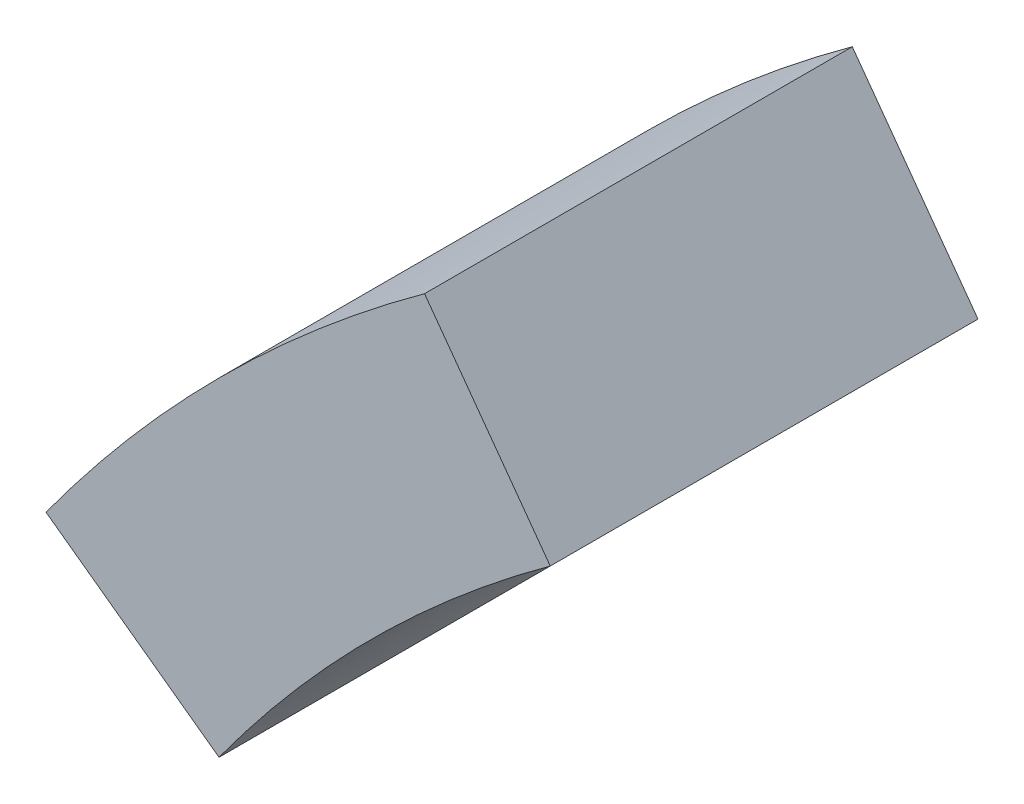
SolidWorks part; units mm, degrees
material "砖"
ref_plane "前视基准面" through (0, 0, 0) normal (0, 0, 1) x (1, 0, 0)
ref_plane "上视基准面" through (0, 0, 0) normal (0, 1, 0) x (1, 0, 0)
ref_plane "右视基准面" through (0, 0, 0) normal (1, 0, 0) x (0, 0, -1)
sketch "草图1" plane through (0, 0, 0) normal (0, 0, 1) x (1, 0, 0)
  line L0 (-4560, 0) -> (-7920, 0)
  line L1 (-12480, 7680) -> (0, 7680)
  line L2 (-12480, 7680) -> (-12480, 0)
  line L3 (-12480, 0) -> (0, 0)
  line L4 (0, 7680) -> (0, 0)
  line L5 (-7920, 0) -> (-7920, 3840)
  line L6 (-7920, 3840) -> (-4560, 3840)
  line L7 (-4560, 3840) -> (-4560, 0)
  line L8 (-7920, 3840) -> (-8160, 3840)
  line L9 (-4560, 3840) -> (-4320, 3840)
  line L10 (-7837.7749, 4359.1486) -> (-8066.0285, 4433.3126)
  line L11 (-7599.1486, 4827.4792) -> (-7793.3126, 4968.5477)
  line L12 (-7227.4792, 5199.1486) -> (-7368.5477, 5393.3126)
  line L13 (-6759.1486, 5437.7749) -> (-6833.3126, 5666.0285)
  line L14 (-6240, 5520) -> (-6240, 5760)
  line L15 (-5720.8514, 5437.7749) -> (-5646.6874, 5666.0285)
  line L16 (-5252.5208, 5199.1486) -> (-5111.4523, 5393.3126)
  line L17 (-4880.8514, 4827.4792) -> (-4686.6874, 4968.5477)
  line L18 (-4642.2251, 4359.1486) -> (-4413.9715, 4433.3126)
  line L19 (-4560, 3840) -> (-4320, 3840)
  line L20 (-4573.7633, 3298.6069) -> (-4560, 3294.1349)
  line L21 (-6833.3126, 5666.0285) -> (-6928.8298, 5960)
  line L22 (-5683.7694, 5551.9017) -> (-5551.1702, 5960)
  line L23 (-5551.1702, 5960) -> (-6928.8298, 5960)
  line L24 (-7920, 0) -> (-9123.3069, 0)
  line L25 (-8160, 0) -> (-8640, 0)
  line L26 (-8160, 0) -> (-8640, 0)
  line L27 (-8640, 3840) -> (-8160, 3840)
  line L28 (-8640, 3840) -> (-8640, 4264)
  line L29 (-7837.7749, 3320.8514) -> (-7920, 3294.1349) [skipped]
  line L30 (-7599.1486, 2852.5208) -> (-7793.3126, 2711.4523) [skipped]
  line L31 (-7227.4792, 2480.8514) -> (-7368.5477, 2286.6874) [skipped]
  line L32 (-6759.1486, 2242.2251) -> (-6833.3126, 2013.9715) [skipped]
  line L33 (-6240, 2160) -> (-6240, 1920) [skipped]
  line L34 (-5720.8514, 2242.2251) -> (-5646.6874, 2013.9715) [skipped]
  line L35 (-5252.5208, 2480.8514) -> (-5111.4523, 2286.6874) [skipped]
  line L36 (-4880.8514, 2852.5208) -> (-4686.6874, 2711.4523) [skipped]
  line L37 (-8640, 4264) -> (-8112.5982, 4264)
  line L38 (-8112.5982, 4264) -> (-8592.5982, 4264)
  line L39 (-8592.5982, 4264) -> (-8592.5982, 4688)
  line L40 (-8592.5982, 4688) -> (-7962.5841, 4688)
  line L41 (-7962.5841, 4688) -> (-8442.5841, 4688)
  line L42 (-8442.5841, 4688) -> (-8442.5841, 5112)
  line L43 (-8442.5841, 5112) -> (-7678.1989, 5112)
  line L44 (-7678.1989, 5112) -> (-8158.1989, 5112)
  line L45 (-8158.1989, 5112) -> (-8158.1989, 5536)
  line L46 (-8158.1989, 5536) -> (-7139.9911, 5536)
  line L47 (-7139.9911, 5536) -> (-7619.9911, 5536)
  line L48 (-7619.9911, 5536) -> (-7619.9911, 5960)
  line L49 (-7619.9911, 5960) -> (-6928.8298, 5960)
  arc A0 (-4560, 3840) -> (-7920, 3840) centre (-6240, 3840) ccw
  arc A1 (-4320, 3840) -> (-8160, 3840) centre (-6240, 3840) ccw
  point P7 (-6240, 0)
  point P56 (-6240, 3840)
  dimension "D5" = 3840
  dimension "D1" = 12480
  dimension "D2" = 7680
  dimension "D3" = 3360
  dimension "D4" = 3840
  dimension "D7" = 240
  dimension "D8" = 480
  dimension "D9" = 424
  dimension "D10" = 720
  dimension "D11" = 480
  dimension "D12" = 480
  dimension "D13" = 480
  dimension "D14" = 480
  dimension "D6" = 20
extrude "凸台-拉伸1" add sketch "草图1" along normal blind 480 contours L12 A1 L11 A0
scale "缩放比例1" scale about origin uniform scaling yes scale factor 1.3
